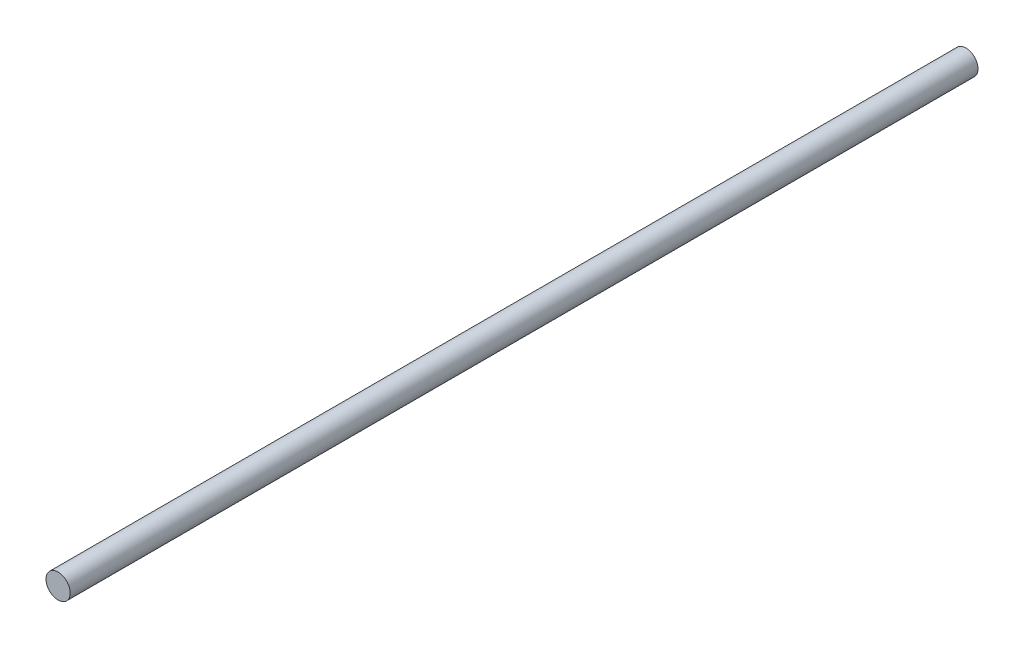
SolidWorks part; units mm, degrees
material "AISI 304"
ref_plane "Front Plane" through (0, 0, 0) normal (0, 0, 1) x (1, 0, 0)
ref_plane "Top Plane" through (0, 0, 0) normal (0, 1, 0) x (1, 0, 0)
ref_plane "Right Plane" through (0, 0, 0) normal (1, 0, 0) x (0, 0, -1)
sketch "Sketch1" plane through (0, 0, 0) normal (0, 0, 1) x (1, 0, 0)
  circle A0 centre (0, 0) radius 2
  dimension "D1" = 4
extrude "Boss-Extrude1" add sketch "Sketch1" along normal mid plane 150
